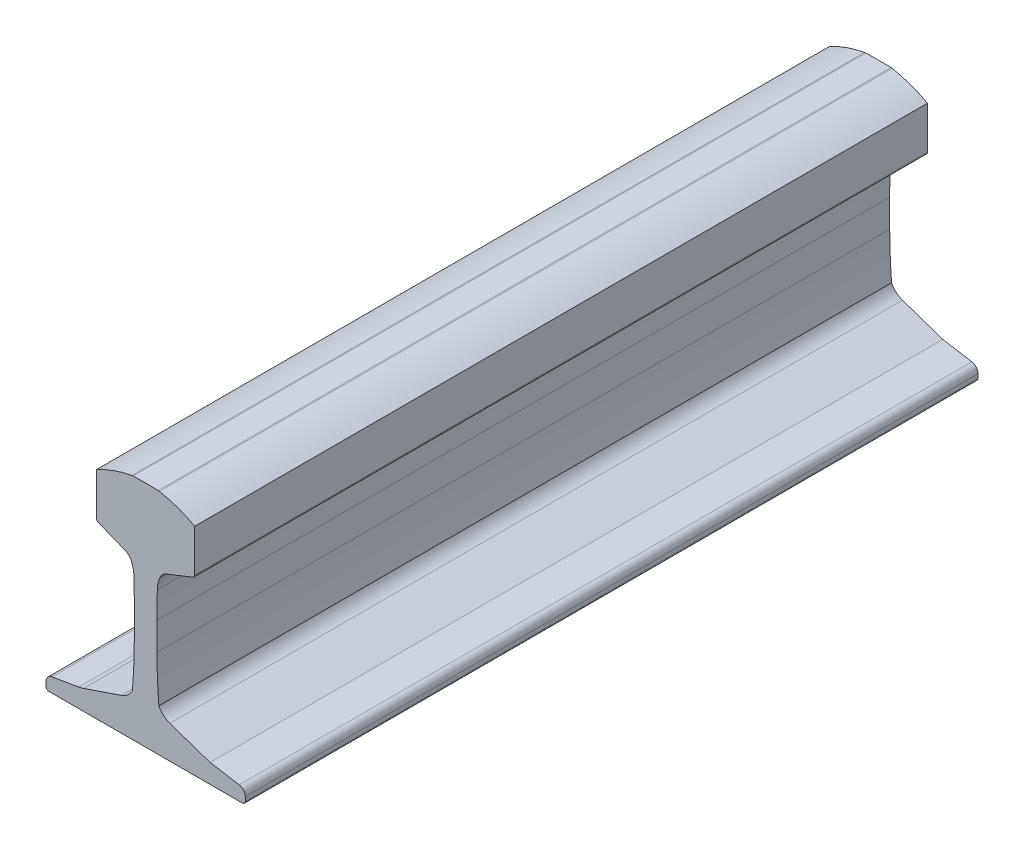
SolidWorks part; units mm, degrees
material "Cast Alloy Steel"
ref_plane "Front Plane" through (0, 0, 0) normal (0, 0, 1) x (1, 0, 0)
ref_plane "Top Plane" through (0, 0, 0) normal (0, 1, 0) x (1, 0, 0)
ref_plane "Right Plane" through (0, 0, 0) normal (1, 0, 0) x (0, 0, -1)
sketch "Sketch3" plane through (0, 0, 0) normal (0, 0, 1) x (1, 0, 0)
  line L0 (0, 0) -> (-66, 0)
  line L1 (-44, 0) -> (-44, 13)
  line L2 (-68, 4.7652) -> (-68, 2)
  line L3 (-63.8218, 9.6972) -> (-45.6274, 12.7288)
  line L4 (0, 0) -> (0, 155.9691) construction
  line L9 (-7.75, 60) -> (-7.75, 79)
  line L10 (-42.439, 13.5342) -> (-16.4793, 22.4179)
  line L11 (0, 0) -> (66, 0)
  line L16 (44, 13) -> (16.4793, 22.4179)
  line L17 (7.75, 60) -> (7.75, 79)
  line L18 (63.8218, 9.6972) -> (44, 13)
  line L19 (68, 4.7652) -> (68, 2)
  line L20 (44, 0) -> (44, 13)
  line L21 (14.0842, 109.4008) -> (32.2387, 116.6169)
  line L33 (-14.0842, 109.4008) -> (-32.2387, 116.6169)
  line L35 (-33.5, 118.4754) -> (-33.5, 147.3393)
  line L36 (33.5, 118.4754) -> (33.5, 147.3393)
  arc A1 (-68, 4.7652) -> (-63.8218, 9.6972) centre (-63, 4.7652) cw
  arc A2 (-66, 0) -> (-68, 2) centre (-66, 2) cw
  arc A6 (-9.0132, 29) -> (-7.75, 60) centre (-388.75, 60) ccw
  arc A7 (-9.0132, 29) -> (-16.4793, 22.4179) centre (-20.6884, 34.7176) cw
  arc A8 (9.0132, 29) -> (16.4793, 22.4179) centre (20.6884, 34.7176) ccw
  arc A9 (9.0132, 29) -> (7.75, 60) centre (388.75, 60) cw
  arc A10 (66, 0) -> (68, 2) centre (66, 2) ccw
  arc A11 (68, 4.7652) -> (63.8218, 9.6972) centre (63, 4.7652) ccw
  arc A13 (-45.6274, 12.7288) -> (-42.439, 13.5342) centre (-48.9146, 32.4568) ccw
  arc A17 (-7.75, 79) -> (-7.9626, 97) centre (-769.75, 79) ccw
  arc A18 (7.75, 79) -> (7.9626, 97) centre (769.75, 79) cw
  arc A19 (-7.7701, 84.5317) -> (-7.75, 84.527) centre (0, 117.1182) ccw construction
  arc A20 (7.75, 84.527) -> (7.7701, 84.5317) centre (0, 117.1182) ccw construction
  arc A22 (-7.9626, 97) -> (-9.6366, 105) centre (-30.4563, 96.4685) ccw
  arc A23 (7.9626, 97) -> (9.6366, 105) centre (30.4563, 96.4685) cw
  arc A26 (-9.6366, 105) -> (-14.0842, 109.4008) centre (-17.0392, 101.9666) ccw
  arc A27 (9.6366, 105) -> (14.0842, 109.4008) centre (17.0392, 101.9666) cw
  arc A28 (-32.2387, 116.6169) -> (-33.5, 118.4754) centre (-31.5, 118.4754) cw
  arc A29 (32.2387, 116.6169) -> (33.5, 118.4754) centre (31.5, 118.4754) ccw
  arc A30 (-33.5, 147.3393) -> (-9.3795, 155.9009) centre (4.9759, 77.1994) cw
  arc A31 (-8.6237, 155.98) -> (8.6237, 155.98) centre (0, -148.898) cw
  arc A32 (33.5, 147.3393) -> (9.3795, 155.9009) centre (-4.9759, 77.1994) ccw
  arc A33 (-8.6237, 155.98) -> (-9.3795, 155.9009) centre (-8.4823, 150.982) ccw
  arc A34 (8.6237, 155.98) -> (9.3795, 155.9009) centre (8.4823, 150.982) cw
  point P3 (-9, 155.9691)
  point P15 (9, 155.9691)
  dimension "D2" = 5
  dimension "D3" = 2
  dimension "D4" = 305
  dimension "D6" = 762
  dimension "D7" = 5
  dimension "D8" = 33.5
  dimension "13" = 13
  dimension "D9" = 22.5
  dimension "D11" = 20
  dimension "D14" = 5
  dimension "D10" = 762
  dimension "D17" = 67
  dimension "D19" = 2
  dimension "D20" = 2
  dimension "D5" = 80
  dimension "D12" = 24
  dimension "D13" = 44
extrude "Boss-Extrude1" add sketch "Sketch3" along normal blind 500 contours L16 A8 A9 L17 A18 A23 A27 L21 A29 L36 A32 A34 A31 A33 A30 L35 A28 L33 A26 A22 A17 L9 A6 A7 L10 A13 L3 A1 L2 A2 L0 L11 A10 L19 A11 L18
